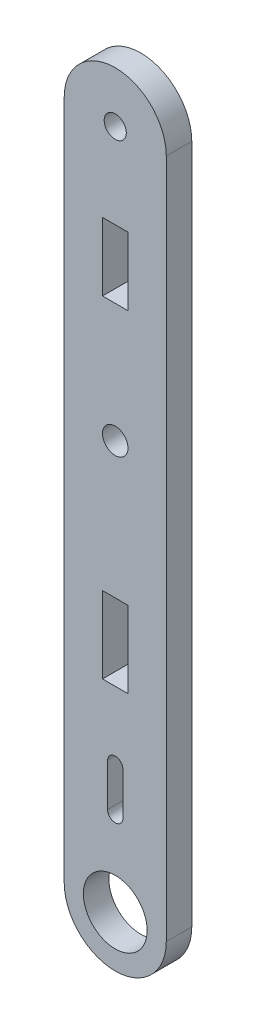
SolidWorks part; units mm, degrees
ref_plane "Front Plane" through (0, 0, 0) normal (0, 0, 1) x (1, 0, 0)
ref_plane "Top Plane" through (0, 0, 0) normal (0, 1, 0) x (1, 0, 0)
ref_plane "Right Plane" through (0, 0, 0) normal (1, 0, 0) x (0, 0, -1)
sketch "Model" plane through (0, 0, 0) normal (0, 0, 1) x (1, 0, 0)
  line L0 (61.1578, 11.1306) -> (61.1578, 6.1305)
  line L1 (62.9578, 6.1305) -> (62.9578, 11.1305)
  line L2 (60.5578, 28.1305) -> (60.5578, 19.1305)
  line L3 (63.5578, 28.1305) -> (63.5578, 19.1305)
  line L4 (60.5578, 66.1305) -> (60.5578, 58.1305)
  line L5 (63.5578, 66.1305) -> (63.5578, 58.1305)
  line L6 (60.5578, 66.1305) -> (63.5578, 66.1305)
  line L7 (60.5578, 58.1305) -> (63.5578, 58.1305)
  line L8 (60.5578, 28.1305) -> (63.5578, 28.1305)
  line L9 (63.5578, 19.1305) -> (60.5578, 19.1305)
  line L10 (56.0578, -3.8695) -> (56.0578, 76.1306)
  line L11 (68.0578, 76.1305) -> (68.0578, -3.8695)
  circle A0 centre (62.0578, -3.8695) radius 3.75
  circle A1 centre (62.0578, 76.1305) radius 1.3
  circle A2 centre (62.0578, 44.1306) radius 1.5
  arc A3 (68.0578, 76.1305) -> (56.0578, 76.1306) centre (62.0578, 76.1306) ccw
  arc A4 (56.0578, -3.8695) -> (68.0578, -3.8695) centre (62.0578, -3.8695) ccw
  arc A5 (61.1578, 6.1305) -> (62.9578, 6.1305) centre (62.0578, 6.1305) ccw
  arc A6 (62.9578, 11.1305) -> (61.1578, 11.1306) centre (62.0578, 11.1306) ccw
extrude "Boss-Extrude1" add sketch "Model" along normal blind 3
